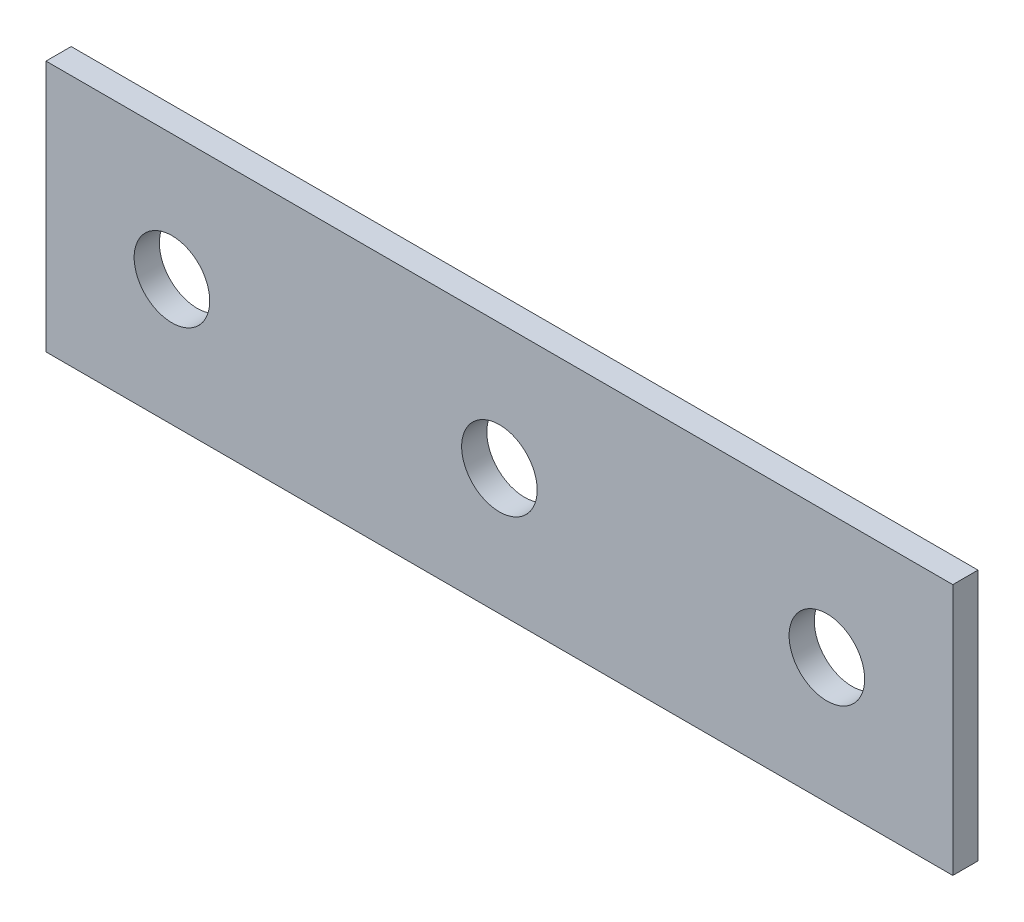
SolidWorks part; units mm, degrees
material "Alloy Steel"
ref_plane "Front Plane" through (0, 0, 0) normal (0, 0, 1) x (1, 0, 0)
ref_plane "Top Plane" through (0, 0, 0) normal (0, 1, 0) x (1, 0, 0)
ref_plane "Right Plane" through (0, 0, 0) normal (1, 0, 0) x (0, 0, -1)
sketch "Sketch1" plane through (0, 0, 0) normal (0, 0, 1) x (1, 0, 0)
  line L1 (-114.3, -31.75) -> (114.3, -31.75)
  line L2 (-114.3, -31.75) -> (-114.3, 31.75)
  line L3 (-114.3, 31.75) -> (114.3, 31.75)
  line L4 (114.3, -31.75) -> (114.3, 31.75)
  line L5 (-114.3, -31.75) -> (114.3, 31.75) construction
  line L6 (-114.3, 31.75) -> (114.3, -31.75) construction
  point P0 (0, 0)
  dimension "D1" = 228.6
  dimension "D2" = 63.5
extrude "Boss-Extrude1" add sketch "Sketch1" along normal blind 6.35
sketch "Sketch2" plane through (0, 0, 6.35) normal (0, 0, 1) x (1, 0, 0)
  line L0 (-114.3, 0) -> (-82.55, 0) construction
  line L1 (-114.3, 31.75) -> (-114.3, -31.75) construction
  circle A0 centre (-82.55, 0) radius 9.525
  dimension "D1" = 19.05
  dimension "D2" = 31.75
extrude "Cut-Extrude1" cut sketch "Sketch2" against normal through all
pattern_linear "LPattern1" count 3 spacing 82.55 along (1, 0, 0) of "Cut-Extrude1"
